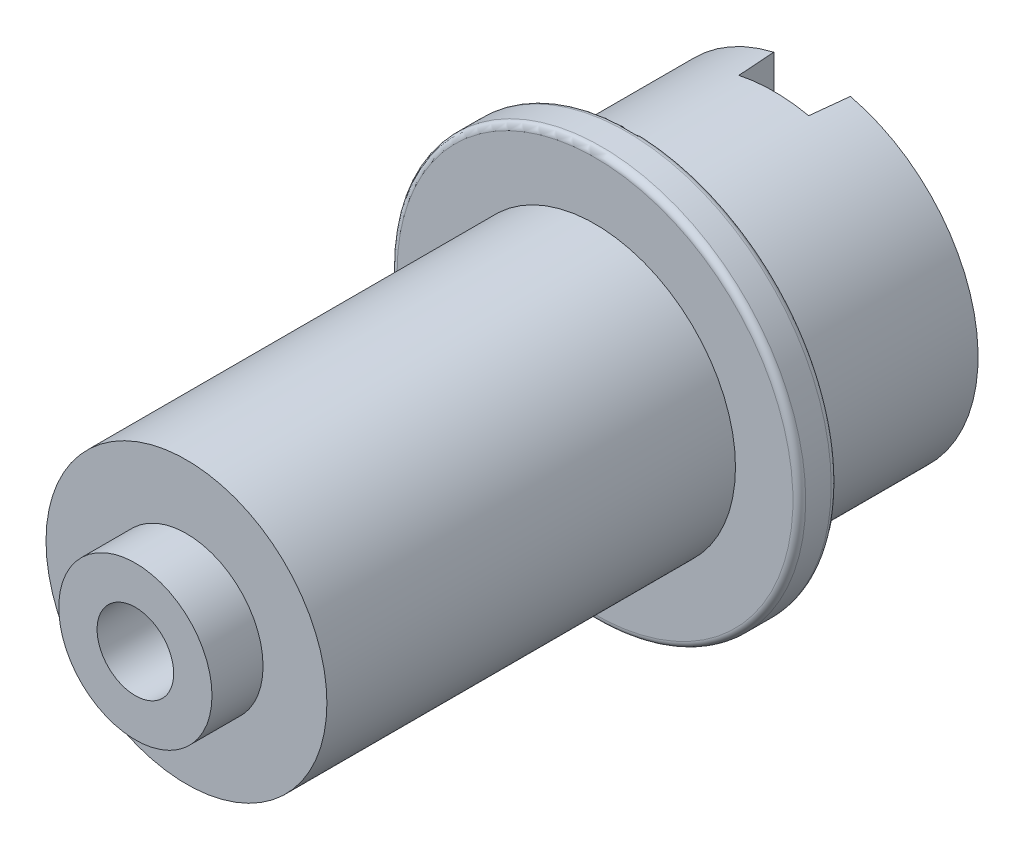
SolidWorks part; units mm, degrees
ref_plane "Plane1" through (0, 0, 0) normal (0, 0, 1) x (1, 0, 0)
ref_plane "Plane2" through (0, 0, 0) normal (0, 1, 0) x (1, 0, 0)
ref_plane "Plane3" through (0, 0, 0) normal (1, 0, 0) x (0, 0, -1)
sketch "Esquisse1" plane through (0, 0, 0) normal (0, 0, 1) x (1, 0, 0)
  circle A0 centre (0, 0) radius 5.5
  dimension "D1" = 11
extrude "Base-Extrusion" add sketch "Esquisse1" along normal blind 16
sketch "Esquisse2" plane through (0, 0, 16) normal (0, 0, 1) x (1, 0, 0)
  circle A0 centre (0, 0) radius 3
  dimension "D1" = 6
extrude "Boss.-Extru.1" add sketch "Esquisse2" along normal blind 2
sketch "Esquisse3" plane through (0, 0, 0) normal (0, 0, -1) x (-1, 0, 0)
  circle A0 centre (0, 0) radius 8
  dimension "D1" = 16
extrude "Boss.-Extru.2" add sketch "Esquisse3" along normal blind 1.5
sketch "Esquisse4" plane through (0, 0, -1.5) normal (0, 0, -1) x (-1, 0, 0)
  circle A0 centre (0, 0) radius 6.5
  dimension "D1" = 13
extrude "Boss.-Extru.3" add sketch "Esquisse4" along normal blind 7
sketch "Esquisse5" plane through (0, 0, -8.5) normal (0, 0, -1) x (-1, 0, 0)
  circle A0 centre (0, 0) radius 4.5
  dimension "D1" = 9
extrude "Enlèv. mat.-Extru.1" cut sketch "Esquisse5" against normal blind 19
sketch "Esquisse6" plane through (0, 0, -8.5) normal (0, 0, -1) x (-1, 0, 0)
  line L0 (0, 0) -> (0, 8) construction
  line L1 (-1.5, 7) -> (-1.5, 3)
  line L2 (1.5, 7) -> (1.5, 3)
  line L3 (-1.5, 3) -> (1.5, 3)
  line L4 (-1.5, 7) -> (1.5, 7)
  dimension "D1" = 3
extrude "Enlèv. mat.-Extru.2" cut sketch "Esquisse6" against normal blind 1.5 draft 5
ref_plane "Plan1" through (0, -5, 0) normal (0, 1, 0) x (-1, 0, 0)
sketch "Esquisse7" plane through (0, -5, 0) normal (0, 1, 0) x (-1, 0, 0)
  line L0 (0, 0) -> (0, -9.3511) construction
  line L1 (0, 16) -> (0, 0) construction
  line L2 (-6.5, -8.5) -> (6.5, -8.5) construction
  line L3 (0, -5) -> (3, -5) construction
  line L4 (0, -5) -> (-3, -5) construction
  line L5 (3, -5) -> (3, -1.5)
  line L6 (-8, -1.5) -> (8, -1.5) construction
  line L7 (-3, -5) -> (-3, -1.5)
  line L8 (3, -1.5) -> (-3, -1.5)
  arc A0 (-3, -5) -> (3, -5) centre (0, -5) ccw
  dimension "D2" = 6
  dimension "D1" = 3.5
extrude "Boss.-Extru.4" add sketch "Esquisse7" against normal blind 2
sketch "Esquisse8" plane through (0, -7, 0) normal (0, -1, 0) x (1, 0, 0)
  circle A0 centre (0, -5) radius 1.5
  dimension "D1" = 3
extrude "Enlèv. mat.-Extru.3" cut sketch "Esquisse8" against normal up to next
sketch "Esquisse9" plane through (0, 0, 18) normal (0, 0, 1) x (1, 0, 0)
  circle A0 centre (0, 0) radius 1.5
  dimension "D1" = 3
extrude "Enlèv. mat.-Extru.4" cut sketch "Esquisse9" against normal through all
fillet "Congé2" radius 0.25
